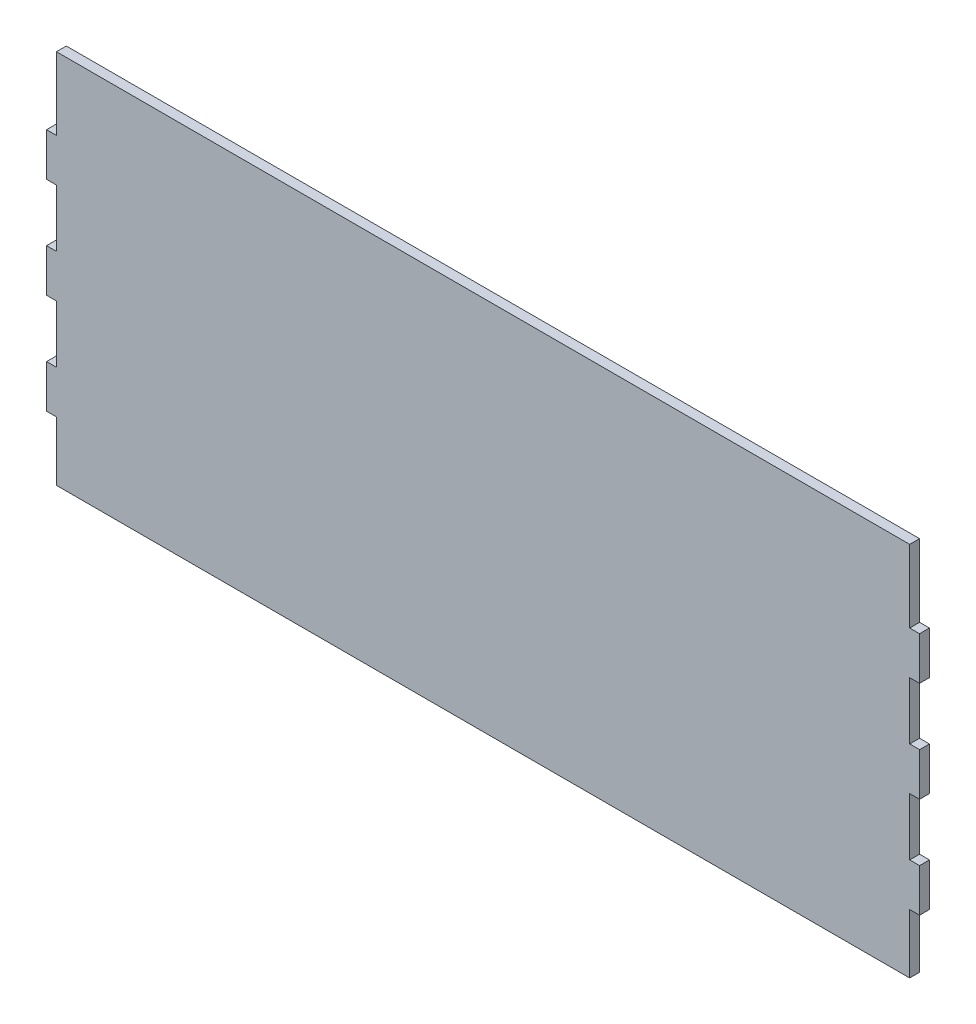
SolidWorks part; units mm, degrees
ref_plane "Front Plane" through (0, 0, 0) normal (0, 0, 1) x (1, 0, 0)
ref_plane "Top Plane" through (0, 0, 0) normal (0, 1, 0) x (1, 0, 0)
ref_plane "Right Plane" through (0, 0, 0) normal (1, 0, 0) x (0, 0, -1)
sketch "Croquis1" plane through (0, 0, 0) normal (0, 0, 1) x (1, 0, 0)
  line L1 (-132.5, 55) -> (132.5, 55)
  line L2 (-132.5, 55) -> (-132.5, -55)
  line L3 (-132.5, -55) -> (132.5, -55)
  line L4 (132.5, 55) -> (132.5, -55)
  line L5 (-132.5, 55) -> (132.5, -55) construction
  line L6 (-132.5, -55) -> (132.5, 55) construction
  point P0 (0, 0)
  dimension "D1" = 265
  dimension "D2" = 110
extrude "Saliente-Extruir1" add sketch "Croquis1" along normal blind 3
sketch "Croquis2" plane through (0, 0, 3) normal (0, 0, 1) x (1, 0, 0)
  line L0 (-132.5, 55) -> (-132.5, -55) construction
  line L1 (-132.5, 37) -> (-129.5, 37)
  line L2 (-132.5, 37) -> (-132.5, 23.9518)
  line L3 (-132.5, 23.9518) -> (-129.5, 23.9518)
  line L6 (-132.5, 6.5241) -> (-132.5, -6.5241)
  line L8 (-132.5, 6.5241) -> (-129.5, 6.5241)
  line L10 (-132.5, -6.5241) -> (-129.5, -6.5241)
  line L11 (-132.5, -23.9518) -> (-132.5, -37)
  line L12 (-132.5, -23.9518) -> (-129.5, -23.9518)
  line L14 (-132.5, -37) -> (-129.5, -37)
  line L15 (-132.5, -55) -> (132.5, -55) construction
  line L16 (132.5, 55) -> (-132.5, 55) construction
  line L17 (0, -55) -> (0, 55) construction
  line L18 (132.5, -23.9518) -> (129.5, -23.9518)
  line L19 (-129.5, -52) -> (129.5, -52)
  line L20 (129.5, -52) -> (129.5, 52)
  line L21 (-129.5, 52) -> (-129.5, -52)
  line L22 (129.5, 52) -> (-129.5, 52)
  line L24 (129.5, -52) -> (129.5, -37)
  line L25 (-129.5, 52) -> (-129.5, 37)
  line L28 (132.5, -37) -> (129.5, -37)
  line L29 (132.5, -23.9518) -> (132.5, -37)
  line L30 (132.5, 6.5241) -> (129.5, 6.5241)
  line L32 (132.5, -6.5241) -> (129.5, -6.5241)
  line L33 (132.5, 6.5241) -> (132.5, -6.5241)
  line L34 (132.5, 23.9518) -> (129.5, 23.9518)
  line L36 (132.5, 37) -> (129.5, 37)
  line L37 (132.5, 37) -> (132.5, 23.9518)
  line L38 (-129.5, 23.9518) -> (-129.5, 6.5241)
  line L39 (-129.5, -6.5241) -> (-129.5, -23.9518)
  line L40 (-129.5, -37) -> (-129.5, -52)
  line L41 (129.5, -23.9518) -> (129.5, -6.5241)
  line L42 (129.5, 6.5241) -> (129.5, 23.9518)
  line L43 (129.5, 37) -> (129.5, 52)
  line L44 (-129.5, 52) -> (-129.5, 55)
  line L45 (129.5, 52) -> (129.5, 55)
  line L46 (-129.5, -52) -> (-129.5, -55)
  line L47 (129.5, -52) -> (129.5, -55)
  line L48 (-129.5, -55) -> (129.5, -55)
  line L49 (-129.5, 55) -> (129.5, 55)
  line M3 (132.5, -55) -> (132.5, 55)
  line M4 (132.5, 55) -> (-132.5, 55)
  line M5 (-132.5, 55) -> (-132.5, -55)
  line M6 (-132.5, -55) -> (132.5, -55)
  dimension "D3" = 18
  dimension "D4" = 18
  dimension "D1" = 3
  dimension "D2" = 3
extrude "Cortar-Extruir1" cut sketch "Croquis2" against normal blind 3 contours L25 L44 L1 M4 M5 | L38 L3 L8 M5 | L45 L43 L36 M3 M4 | L42 L30 L34 M3 | L41 L18 L32 M3 | L24 L47 L28 M6 M3 | L39 L10 L12 M5 | L46 L40 L14 M5 M6
sketch "Croquis4" plane through (0, 0, 0) normal (0, 0, -1) x (-1, 0, 0)
  line L6 (129.5, 55) -> (129.5, 37) construction
  line L7 (-129.5, 55) -> (129.5, 55)
  line L8 (-129.5, 55) -> (-129.5, 59)
  line L9 (-129.5, 59) -> (129.5, 59)
  line L10 (129.5, 55) -> (129.5, 59)
  dimension "D1" = 4
extrude "Saliente-Extruir3" add sketch "Croquis4" against normal blind 3
sketch "Croquis6" plane through (0, 0, 0) normal (0, 0, -1) x (-1, 0, 0)
  line L0 (-100.0921, -10.7078) -> (100.0921, -10.7078) construction
  text T0 "ITAM MANTIS" font "Century Gothic" height 25
  point P2 (0, -10.7078)
